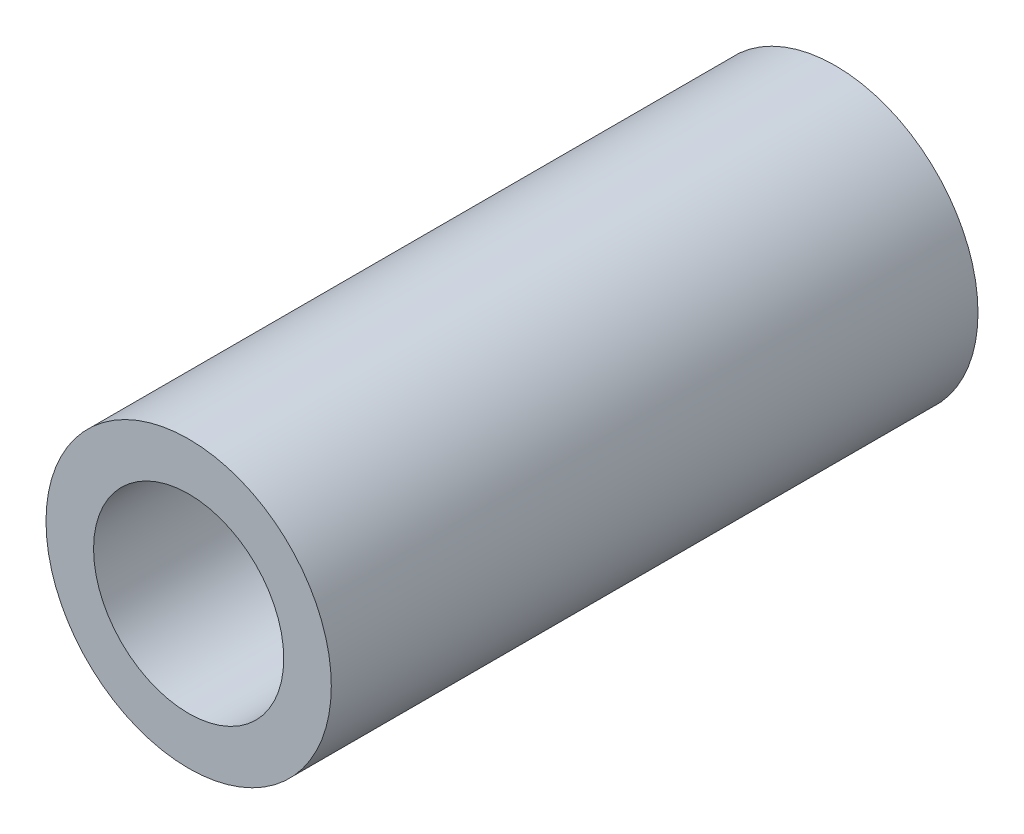
SolidWorks part; units mm, degrees
ref_plane "Front Plane" through (0, 0, 0) normal (0, 0, 1) x (1, 0, 0)
ref_plane "Top Plane" through (0, 0, 0) normal (0, 1, 0) x (1, 0, 0)
ref_plane "Right Plane" through (0, 0, 0) normal (1, 0, 0) x (0, 0, -1)
sketch "Эскиз1" plane through (0, 0, 0) normal (0, 0, 1) x (1, 0, 0)
  circle A0 centre (0, 0) radius 1.5
  circle A1 centre (0, 0) radius 1
  dimension "D1" = 3
  dimension "D2" = 2
extrude "Бобышка-Вытянуть1" add sketch "Эскиз1" along normal mid plane 6.8
equation "\"D1@Бобышка-Вытянуть1\"=10-3.2"
